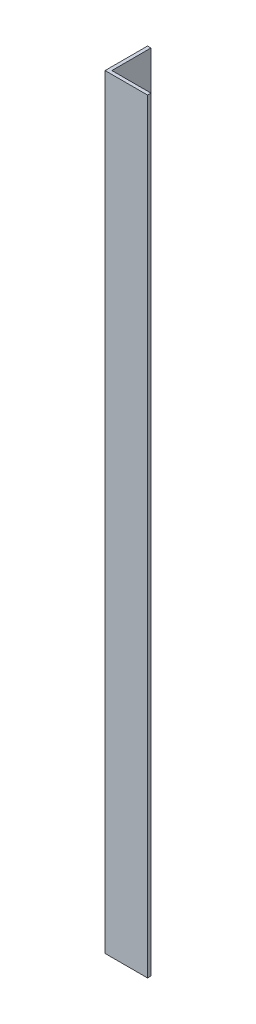
SolidWorks part; units mm, degrees
ref_plane "Спереди" through (0, 0, 0) normal (0, 0, 1) x (1, 0, 0)
ref_plane "Сверху" through (0, 0, 0) normal (0, 1, 0) x (1, 0, 0)
ref_plane "Справа" through (0, 0, 0) normal (1, 0, 0) x (0, 0, -1)
sketch "Эскиз1" plane through (0, 0, 0) normal (0, 1, 0) x (1, 0, 0)
  line L0 (0, 50) -> (0, 0)
  line L1 (0, 0) -> (50, 0)
extrude "Вытянуть-Тонкостенный1" add sketch "Эскиз1" along normal blind 900 thin thin type one direction reverse wall 4
